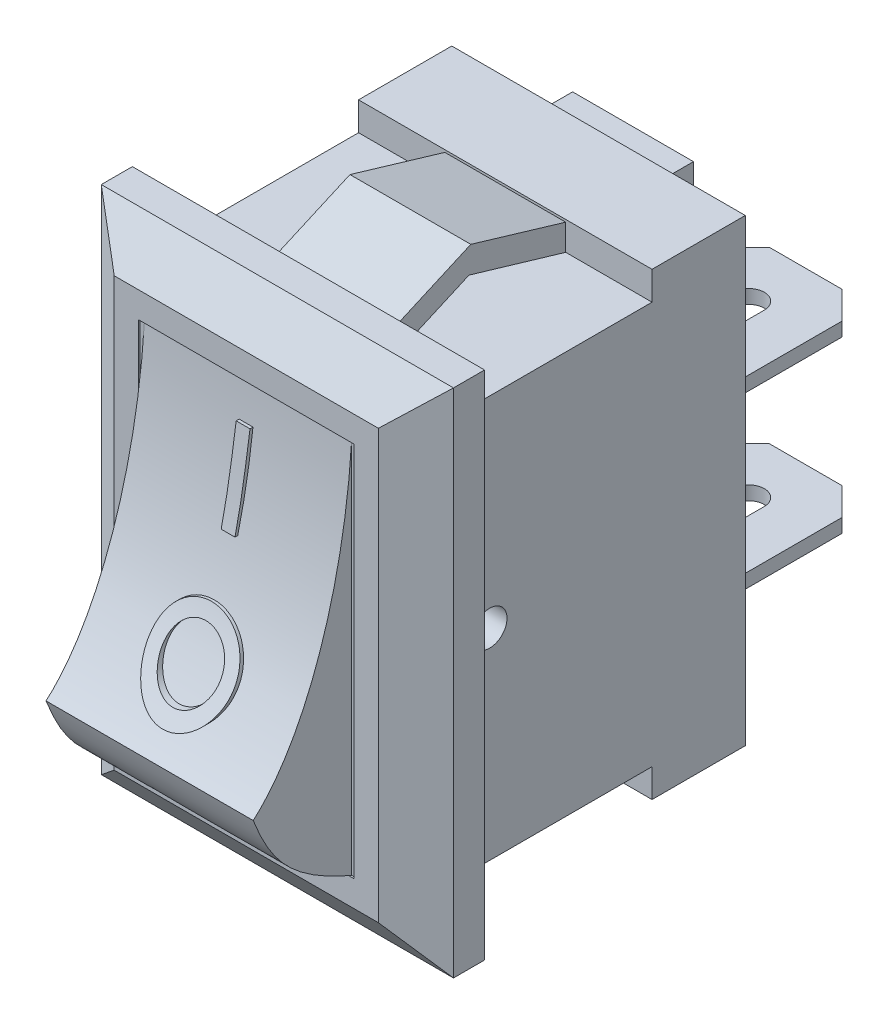
SolidWorks part; units mm, degrees
ref_plane "Front Plane" through (0, 0, 0) normal (0, 0, 1) x (1, 0, 0)
ref_plane "Top Plane" through (0, 0, 0) normal (0, 1, 0) x (1, 0, 0)
ref_plane "Right Plane" through (0, 0, 0) normal (1, 0, 0) x (0, 0, -1)
sketch "Sketch1" plane through (0, 0, 0) normal (0, 0, 1) x (1, 0, 0)
  line L1 (5.1, -7.4) -> (-5.1, -7.4)
  line L2 (5.1, -7.4) -> (5.1, 7.4)
  line L3 (5.1, 7.4) -> (-5.1, 7.4)
  line L4 (-5.1, -7.4) -> (-5.1, 7.4)
  line L5 (5.1, -7.4) -> (-5.1, 7.4) construction
  line L6 (5.1, 7.4) -> (-5.1, -7.4) construction
  point P0 (0, 0)
  dimension "D1" = 10.2
  dimension "D2" = 14.8
extrude "Boss-Extrude1" add sketch "Sketch1" along normal blind 1.8
sketch "Sketch2" plane through (0, 0, 1.8) normal (0, 0, 1) x (1, 0, 0)
  line L1 (3.125, -5.45) -> (-3.125, -5.45)
  line L2 (3.125, -5.45) -> (3.125, 5.45)
  line L3 (3.125, 5.45) -> (-3.125, 5.45)
  line L4 (-3.125, -5.45) -> (-3.125, 5.45)
  line L5 (3.125, -5.45) -> (-3.125, 5.45) construction
  line L6 (3.125, 5.45) -> (-3.125, -5.45) construction
  point P0 (0, 0)
  dimension "D1" = 6.25
  dimension "D2" = 10.9
extrude "Cut-Extrude1" cut sketch "Sketch2" against normal blind 0.05
sketch "Sketch3" plane through (0, 0, 1.8) normal (0, 0, 1) x (1, 0, 0)
  line L1 (3.825, -6.15) -> (-3.825, -6.15) construction
  line L2 (3.825, -6.15) -> (3.825, 6.15) construction
  line L3 (3.825, 6.15) -> (-3.825, 6.15) construction
  line L4 (-3.825, -6.15) -> (-3.825, 6.15) construction
  line L5 (3.825, -6.15) -> (-3.825, 6.15) construction
  line L6 (3.825, 6.15) -> (-3.825, -6.15) construction
  line L7 (3.125, 5.45) -> (-3.125, 5.45) construction
  line L8 (-3.125, 5.45) -> (-3.125, -5.45) construction
  line L9 (3.125, -5.45) -> (3.125, 5.45) construction
  line L10 (-3.125, -5.45) -> (3.125, -5.45) construction
  point P0 (0, 0)
  dimension "D1" = 0.7
  dimension "D2" = 0.7
  dimension "D3" = 0.7
  dimension "D4" = 0.7
sketch "Sketch4" plane through (0, 0, 0) normal (1, 0, 0) x (0, 0, -1)
  line L0 (-1.8, 6.2) -> (-0.9, 7.4)
  line L1 (-1.8, -6.15) -> (-1.8, 6.15) construction
  line L2 (-1.8, -7.4) -> (-1.8, 7.4) construction
  line L3 (-1.8, 7.4) -> (0, 7.4) construction
  line L4 (-0.9, 7.4) -> (-1.8, 7.4)
  line L5 (-1.8, 7.4) -> (-1.8, 6.2)
  dimension "D1" = 1.2
extrude "Cut-Extrude2" cut sketch "Sketch4" against normal through all and the other way through all contours L0 L4 L5
mirror "Mirror1" about plane through (0, 0, 0) normal (0, 1, 0) of "Cut-Extrude2"
sketch "Sketch5" plane through (0, 0, 0) normal (0, 1, 0) x (1, 0, 0)
  line L0 (-5.1, -1.8) -> (-3.825, -1.8)
  line L1 (3.825, -1.8) -> (-3.825, -1.8) construction
  line L2 (-5.1, -1.8) -> (5.1, -1.8) construction
  line L3 (-3.825, -1.8) -> (-5.1, -0.9)
  line L4 (-5.1, -0.9) -> (-5.1, -1.8)
extrude "Cut-Extrude3" cut sketch "Sketch5" against normal through all and the other way through all
mirror "Mirror2" about plane through (0, 0, 0) normal (1, 0, 0) of "Cut-Extrude3"
sketch "Sketch6" plane through (0, 0, 0) normal (1, 0, 0) x (0, 0, -1)
  line L0 (0, 5.825) -> (5.7, 5.825)
  line L1 (0, 5.61) -> (0, -5.61) construction
  line L2 (5.7, 5.825) -> (5.7, 6.65)
  line L3 (5.7, 6.65) -> (8.4, 6.65)
  line L4 (8.4, 6.65) -> (8.4, -6.65)
  line L5 (8.4, -6.65) -> (5.7, -6.65)
  line L6 (5.7, -6.65) -> (5.7, -5.825)
  line L7 (5.7, -5.825) -> (0, -5.825)
  line L8 (0, 0) -> (8.4, 0) construction
  line L9 (0, 5.825) -> (0, -5.825)
  dimension "D1" = 5.7
  dimension "D2" = 2.7
  dimension "D3" = 11.65
  dimension "D4" = 13.3
extrude "Boss-Extrude2" add sketch "Sketch6" along normal blind 4.25 and the other way blind 4.25
sketch "Sketch7" plane through (0, 0, -8.4) normal (0, 0, -1) x (-1, 0, 0)
  line L0 (0, 5.61) -> (0, -5.61) construction
  line L1 (1.75, 3.6) -> (-1.75, 3.6)
  line L2 (1.75, 3.6) -> (1.75, 6.25)
  line L3 (1.75, 6.25) -> (-1.75, 6.25)
  line L4 (-1.75, 3.6) -> (-1.75, 6.25)
  line L5 (1.75, 3.6) -> (-1.75, 6.25) construction
  line L6 (1.75, 6.25) -> (-1.75, 3.6) construction
  line L7 (4.25, 6.65) -> (-4.25, 6.65) construction
  line L8 (1.75, -1.325) -> (-1.75, -1.325)
  line L9 (1.75, -1.325) -> (1.75, 1.325)
  line L10 (1.75, 1.325) -> (-1.75, 1.325)
  line L11 (-1.75, -1.325) -> (-1.75, 1.325)
  line L12 (1.75, -1.325) -> (-1.75, 1.325) construction
  line L13 (1.75, 1.325) -> (-1.75, -1.325) construction
  line L14 (1.75, -6.25) -> (-1.75, -6.25)
  line L15 (1.75, -6.25) -> (1.75, -3.6)
  line L16 (1.75, -3.6) -> (-1.75, -3.6)
  line L17 (-1.75, -6.25) -> (-1.75, -3.6)
  line L18 (1.75, -6.25) -> (-1.75, -3.6) construction
  line L19 (1.75, -3.6) -> (-1.75, -6.25) construction
  line L20 (4.25, -6.65) -> (-4.25, -6.65) construction
  line L21 (5.61, 0) -> (-5.61, 0) construction
  point P0 (0, 4.925)
  point P7 (0, 0)
  point P12 (0, -4.925)
  dimension "D1" = 2.65
  dimension "D2" = 0.4
  dimension "D3" = 3.5
  dimension "D4" = 0.4
extrude "Boss-Extrude3" add sketch "Sketch7" along normal blind 1
sketch "Sketch8" plane through (0, 0, -8.4) normal (0, 0, -1) x (-1, 0, 0)
  line L0 (0, 6.16) -> (0, -6.16) construction
  line L1 (3.35, 3.6) -> (-3.35, 3.6)
  line L2 (3.35, 3.6) -> (3.35, 6.25)
  line L3 (3.35, 6.25) -> (-3.35, 6.25)
  line L4 (-3.35, 3.6) -> (-3.35, 6.25)
  line L5 (3.35, 3.6) -> (-3.35, 6.25) construction
  line L6 (3.35, 6.25) -> (-3.35, 3.6) construction
  line L7 (-1.75, 6.25) -> (-1.75, 3.6) construction
  line L8 (3.35, -1.325) -> (-3.35, -1.325)
  line L9 (3.35, -1.325) -> (3.35, 1.325)
  line L10 (3.35, 1.325) -> (-3.35, 1.325)
  line L11 (-3.35, -1.325) -> (-3.35, 1.325)
  line L12 (3.35, -1.325) -> (-3.35, 1.325) construction
  line L13 (3.35, 1.325) -> (-3.35, -1.325) construction
  line L14 (3.35, -6.25) -> (-3.35, -6.25)
  line L15 (3.35, -6.25) -> (3.35, -3.6)
  line L16 (3.35, -3.6) -> (-3.35, -3.6)
  line L17 (-3.35, -6.25) -> (-3.35, -3.6)
  line L18 (3.35, -6.25) -> (-3.35, -3.6) construction
  line L19 (3.35, -3.6) -> (-3.35, -6.25) construction
  line L20 (-1.75, 3.6) -> (1.75, 3.6) construction
  line L21 (1.75, -3.6) -> (-1.75, -3.6) construction
  point P0 (0, 4.925)
  point P7 (0, 0)
  point P13 (0, -4.925)
  dimension "D1" = 6.7
extrude "Boss-Extrude4" add sketch "Sketch8" along normal blind 0.2
sketch "Sketch10" plane through (0, 0, -9.4) normal (0, 0, -1) x (-1, 0, 0)
  line L0 (-1.75, 4.925) -> (1.75, 4.925) construction
  line L1 (-1.75, 6.25) -> (-1.75, 3.6) construction
  line L2 (1.75, 3.6) -> (1.75, 6.25) construction
sketch "Sketch12" plane through (0, 0, -9.4) normal (0, 0, -1) x (-1, 0, 0)
  line L0 (-1.75, -4.925) -> (1.75, -4.925) construction
  line L1 (-1.75, -3.6) -> (-1.75, -6.25) construction
  line L2 (1.75, -6.25) -> (1.75, -3.6) construction
  line L3 (-1.75, 4.925) -> (1.75, 4.925) construction
  line L5 (1.85, 5.125) -> (-1.85, 5.125) construction
  line L6 (1.85, 5.125) -> (1.85, 4.725) construction
  line L7 (1.85, 4.725) -> (-1.85, 4.725) construction
  line L8 (-1.85, 5.125) -> (-1.85, 4.725) construction
  line L9 (1.85, 5.125) -> (-1.85, 4.725) construction
  line L10 (1.85, 4.725) -> (-1.85, 5.125) construction
  line L11 (1.85, 0.2) -> (-1.85, 0.2)
  line L12 (1.85, 0.2) -> (1.85, -0.2)
  line L13 (1.85, -0.2) -> (-1.85, -0.2)
  line L14 (-1.85, 0.2) -> (-1.85, -0.2)
  line L15 (1.85, 0.2) -> (-1.85, -0.2) construction
  line L16 (1.85, -0.2) -> (-1.85, 0.2) construction
  line L17 (1.85, -5.125) -> (-1.85, -5.125)
  line L18 (1.85, -5.125) -> (1.85, -4.725)
  line L19 (1.85, -4.725) -> (-1.85, -4.725)
  line L20 (-1.85, -5.125) -> (-1.85, -4.725)
  line L21 (1.85, -5.125) -> (-1.85, -4.725) construction
  line L22 (1.85, -4.725) -> (-1.85, -5.125) construction
  point P6 (0, 0)
  point P7 (0, 4.925)
  point P8 (0, 4.925)
  point P11 (0, -4.925)
  point P22 (0, -4.925)
  dimension "D1" = 3.7
  dimension "D2" = 0.4
extrude "Boss-Extrude5" add sketch "Sketch12" along normal blind 5 and the other way blind 1.5
chamfer "Chamfer1" distance 0.8 angle 45 8 edges at (-1.85, -4.925, -8.6) (-1.85, 0, -8.6) (1.85, -4.925, -8.6) (1.85, 0, -8.6) (1.85, -4.925, -14.4) (-1.85, -4.925, -14.4) (-1.85, 0, -14.4) (1.85, 0, -14.4)
sketch "Sketch13" plane through (0, 0.2, 0) normal (0, 1, 0) x (1, 0, 0)
  line L0 (0, 12.75) -> (0, 11.55) construction
  line L1 (0, -8.14) -> (0, 8.14) construction
  line L2 (0.45, 12.75) -> (0.45, 11.55)
  line L3 (-0.45, 12.75) -> (-0.45, 11.55)
  line L4 (-1.85, 9.4) -> (-1.85, 13.6) construction
  line L5 (1.85, 9.4) -> (1.85, 13.6) construction
  line L6 (-1.05, 14.4) -> (1.05, 14.4) construction
  line L7 (1.75, 9.4) -> (-1.75, 9.4) construction
  arc A0 (0.45, 12.75) -> (-0.45, 12.75) centre (0, 12.75) ccw
  arc A1 (-0.45, 11.55) -> (0.45, 11.55) centre (0, 11.55) ccw
  point P5 (0, 12.15)
  point P14 (0, 13.2)
  point P17 (0, 11.1)
  dimension "D1" = 1.4
  dimension "D2" = 1.4
  dimension "D3" = 1.2
  dimension "D4" = 1.7
extrude "Cut-Extrude4" cut sketch "Sketch13" against normal through all
sketch "Sketch14" plane through (0, 0, 0) normal (1, 0, 0) x (0, 0, -1)
  line L0 (5.7, 6.5819) -> (2.9512, 7.4)
  line L1 (2.9512, 7.4) -> (0, 6.0966)
  line L2 (0, 5.61) -> (0, -5.61) construction
  line L3 (5.7, 6.65) -> (5.7, 5.825) construction
  line L5 (1.0221, 5.825) -> (2.8985, 6.6537)
  line L6 (2.8985, 6.6537) -> (5.7, 5.825)
  line L7 (0, 6.0966) -> (0, 5.825)
  line L8 (5.61, 0) -> (-5.61, 0) construction
  line L9 (5.7, 5.825) -> (0, 5.825) construction
  line L10 (0, 5.825) -> (1.0221, 5.825)
  line L11 (5.7, 6.5819) -> (5.7, 5.825)
  dimension "D1" = 7.4
extrude "Boss-Extrude6" add sketch "Sketch14" along normal blind 1.75 and the other way blind 1.75
mirror "Mirror3" about plane through (0, 0, 0) normal (0, 1, 0) of "Boss-Extrude6"
sketch "Sketch15" plane through (4.25, 0, 0) normal (1, 0, 0) x (0, 0, -1)
  line L0 (5.61, 0) -> (-5.61, 0) construction
  line L1 (0, 5.61) -> (0, -5.61) construction
  circle A0 centre (1, 0) radius 0.5
  dimension "D1" = 1
  dimension "D2" = 1
extrude "Cut-Extrude5" cut sketch "Sketch15" against normal blind 1
mirror "Mirror4" about plane through (0, 0, 0) normal (1, 0, 0) of "Cut-Extrude5"
sketch "Sketch16" plane through (0, 0, 0) normal (1, 0, 0) x (0, 0, -1)
  line L0 (-1.8, 6.15) -> (-1.8, -6.15) construction
  line L1 (-1.75, -5.45) -> (-1.8, -5.45) construction
  line L2 (-1.75, 5.45) -> (-1.75, -5.45)
  spline S0 degree 3 poles (-4.6, -2.65) (-3.0458, -1.2904) (-1.9674, 1.9693) (-1.75, 5.45) knots 0 0 0 0 1 1 1 1
  spline S1 degree 3 poles (-1.75, -5.45) (-3.5299, -4.6987) (-4.114, -3.8972) (-4.6, -2.65) knots 0 0 0 0 1 1 1 1
  point P0 (-4.6, -2.65)
  point P3 (-1.775, -5.45)
  dimension "D1" = 2.8
  dimension "D2" = 2.8
extrude "Boss-Extrude7" add sketch "Sketch16" along normal blind 3 and the other way blind 3
sketch3d "3DSketch1" plane through (0, 0, 0) normal (0, 0, 1) x (1, 0, 0)
  dimension "D1" = 0.01
sketch "Sketch17" plane through (0, 0, 1.81) normal (0, 0, 1) x (1, 0, 0)
  line L0 (-3, 5.45) -> (3, 5.45) construction
  line L1 (0.2294, 1.95) -> (-0.1706, 1.95)
  line L2 (0.2294, 1.95) -> (0.2294, 4.45)
  line L3 (0.2294, 4.45) -> (-0.1706, 4.45)
  line L4 (-0.1706, 1.95) -> (-0.1706, 4.45)
  line L5 (0.2294, 1.95) -> (-0.1706, 4.45) construction
  line L6 (0.2294, 4.45) -> (-0.1706, 1.95) construction
  circle A0 centre (0, -0.8) radius 1.25
  circle A1 centre (0, -0.8) radius 0.85
  point P0 (0.0294, 3.2)
  point P10 (0, 0.45)
  dimension "D2" = 0.4
  dimension "D5" = 2.5
  dimension "D1" = 0.4
  dimension "D3" = 1
  dimension "D4" = 1.5
  dimension "D6" = 2.5
extrude "Boss-Extrude10" add sketch "Sketch17" along normal blind 3
sketch "Sketch18" plane through (3, 0, 0) normal (1, 0, 0) x (0, 0, -1)
  line L0 (-1.8, -6.15) -> (-1.8, 6.15) construction
  line L1 (-0.9, -7.4) -> (-0.9, 7.4) construction
  line L2 (-1.9, 4.6086) -> (-5.8779, 4.6086)
  line L3 (-5.8779, 4.6086) -> (-5.8779, -2.3978)
  line L4 (-5.8779, -2.3978) -> (-4.5, -2.3978)
  spline S0 degree 3 poles (-1.9, 4.6086) (-2.2903, 1.8686) (-2.6091, -0.1202) (-4.5, -2.3978) knots 0 0 0 0 1 1 1 1
  dimension "D1" = 0.1
  dimension "D2" = 3.6
extrude "Cut-Extrude6" cut sketch "Sketch18" against normal through all
sketch "Sketch19" plane through (0, -5.125, 0) normal (0, -1, 0) x (1, 0, 0)
  line L0 (0, -11.1) -> (0, -13.2) construction
  line L1 (0, -13.2) -> (0, -16.2679) construction
  arc A0 (0.45, -11.55) -> (-0.45, -11.55) centre (0, -11.55) ccw construction
  arc A1 (-0.45, -12.75) -> (0.45, -12.75) centre (0, -12.75) ccw construction
sketch "Sketch20" plane through (0, -0.2, 0) normal (0, -1, 0) x (1, 0, 0)
  line L0 (0, -11.1) -> (0, -13.2) construction
  line L1 (0, -13.2) -> (0, -16.3459) construction
  arc A0 (0.45, -11.55) -> (-0.45, -11.55) centre (0, -11.55) ccw construction
  arc A1 (-0.45, -12.75) -> (0.45, -12.75) centre (0, -12.75) ccw construction
equation "\"D2@Sketch3\"=\"D1@Sketch3\""
